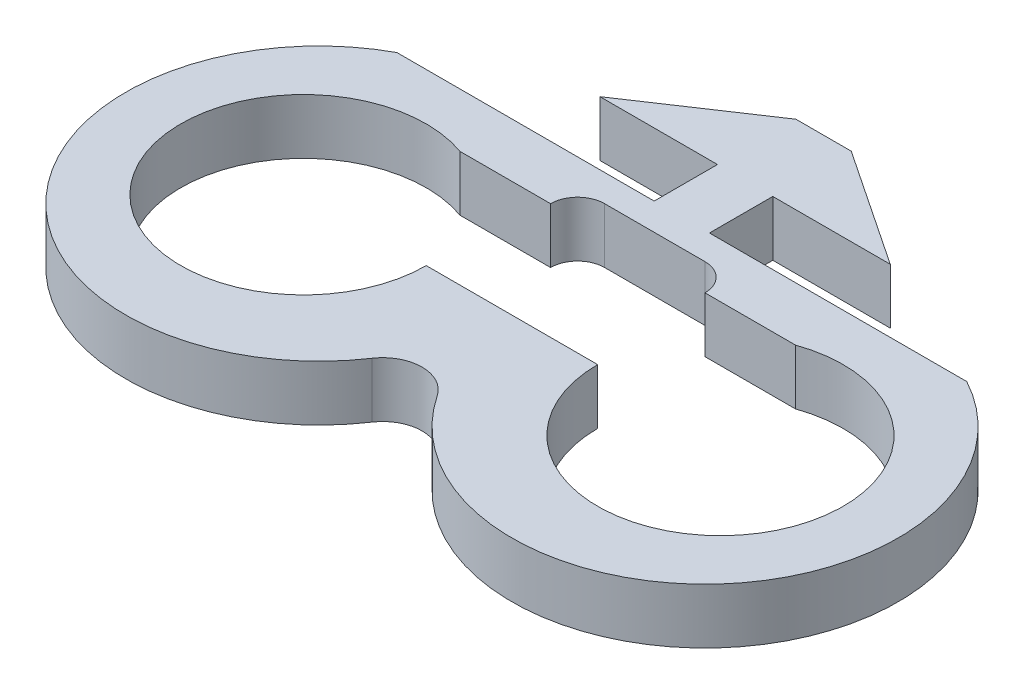
SolidWorks part; units mm, degrees
ref_plane "Front" through (0, 0, 0) normal (0, 0, 1) x (1, 0, 0)
ref_plane "Top" through (0, 0, 0) normal (0, 1, 0) x (1, 0, 0)
ref_plane "Right" through (0, 0, 0) normal (1, 0, 0) x (0, 0, -1)
sketch "Sketch1" plane through (0, 0, 0) normal (0, 1, 0) x (1, 0, 0)
  line L0 (-1.7907, 2.05) -> (-9.398, 2.05)
  line L2 (-1.7907, -2.05) -> (-1.7907, 2.05)
  line L4 (1.7907, -2.05) -> (1.7907, 2.05)
  line L7 (-9.398, 2.05) -> (-1.7907, 7.13)
  line L8 (-1.7907, 7.13) -> (1.7907, 7.13)
  line L9 (1.7907, 7.13) -> (9.398, 2.05)
  line L10 (9.398, 2.05) -> (1.7907, 2.05)
  line L11 (1.7907, -2.05) -> (25.0063, -2.05)
  line L12 (-1.7907, -2.05) -> (-25.0063, -2.05)
  line L13 (-25.0063, -2.05) -> (-25.0063, -13.0482)
  line L14 (-25.0063, -13.0482) -> (25.0063, -13.0482)
  line L15 (25.0063, -13.0482) -> (25.0063, -2.05)
  line L16 (25.0063, -2.05) -> (1.7907, -2.05)
  point P0 (0, 0)
  point P17 (0, 7.13)
  point P19 (0, -13.0482)
  point P24 (1.7907, 0)
  dimension "D1" = 18.796
  dimension "D2" = 3.5814
  dimension "D3" = 50.0126
  dimension "D4" = 10.9982
  dimension "D5" = 5.08
  dimension "D7" = 4.1
extrude "Boss-Extrude1" add sketch "Sketch1" along normal blind 3.5814 contours L14 L15 L11 L4 L10 L9 L8 L7 L0 L2 L12 L13
sketch "Sketch3" plane through (0, 3.5814, 0) normal (0, 1, 0) x (1, 0, 0)
  line L3 (-25.0063, -13.0482) -> (25.0063, -13.0482) construction
  line L16 (-25.0063, -13.0482) -> (25.0063, -13.0482)
  line L17 (25.0063, -13.0482) -> (25.0063, -2.05)
  line L18 (25.0063, -2.05) -> (1.7907, -2.05)
  line L19 (1.7907, -2.05) -> (1.7907, 2.05)
  line L20 (1.7907, 2.05) -> (9.398, 2.05)
  line L21 (9.398, 2.05) -> (1.7907, 7.13)
  line L22 (1.7907, 7.13) -> (-1.7907, 7.13)
  line L23 (-1.7907, 7.13) -> (-9.398, 2.05)
  line L24 (-9.398, 2.05) -> (-1.7907, 2.05)
  line L25 (-1.7907, 2.05) -> (-1.7907, -2.05)
  line L26 (-1.7907, -2.05) -> (-25.0063, -2.05)
  line L27 (-25.0063, -2.05) -> (-25.0063, -13.0482)
  line L28 (-25.0063, -13.0482) -> (25.0063, -13.0482)
  arc A2 (-25.0063, -13.0482) -> (-2.1111, -20.0005) centre (-12.5031, -13.0482) ccw
  arc A3 (2.1111, -20.0005) -> (25.0063, -13.0482) centre (12.5032, -13.0482) ccw
  arc A4 (2.1111, -20.0005) -> (-2.1111, -20.0005) centre (0, -21.4129) ccw
  point P14 (0, -13.0482)
  line M15 (-25.0063, -13.0482) -> (25.0063, -13.0482)
  dimension "D2" = 2.54
  dimension "D1" = 0
extrude "Boss-Extrude2" add sketch "Sketch3" against normal up to surface (3.5814 mm away) contours A2 M15 | L28 A3 up to face at (0, 0, 0.9864)
sketch "Sketch4" plane through (0, 3.5814, 0) normal (0, 1, 0) x (1, 0, 0)
  line L0 (-1025.0063, -13.0482) -> (48974.9937, -13.0482) construction
  circle A0 centre (-13.5, -13.0482) radius 7.95
  circle A1 centre (13.5, -13.0482) radius 7.95
  dimension "D1" = 15.9
  dimension "D2" = 13.5
  dimension "D3" = 13.5
extrude "Cut-Extrude2" cut sketch "Sketch4" against normal through all
sketch "Sketch5" plane through (0, 3.5814, 0) normal (0, 1, 0) x (1, 0, 0)
  line L2 (-3.25, -5.55) -> (3.25, -5.55) construction
  line L3 (-3.25, -3.8) -> (3.25, -3.8)
  line L5 (1.7907, -2.05) -> (25.0063, -2.05) construction
  line L8 (-5, -5.55) -> (-10.8581, -5.55)
  line L9 (5, -5.55) -> (10.8581, -5.55)
  line L10 (-5.55, -13.0482) -> (5.55, -13.0482)
  circle A0 centre (-13.5, -13.0482) radius 7.95 construction
  circle A1 centre (13.5, -13.0482) radius 7.95 construction
  arc A3 (-3.25, -3.8) -> (-5, -5.55) centre (-3.25, -5.55) ccw
  arc A4 (5, -5.55) -> (3.25, -3.8) centre (3.25, -5.55) ccw
  arc A8 (10.8581, -5.55) -> (5.55, -13.0482) centre (13.5, -13.0482) ccw
  arc A9 (-5.55, -13.0482) -> (-10.8581, -5.55) centre (-13.5, -13.0482) ccw
  point P7 (0, -5.55)
  point P12 (0, -15.5882)
  point P28 (0, -10.5082)
  dimension "D3" = 2.54
  dimension "D5" = 1.75
  dimension "D10" = 2.54
extrude "Cut-Extrude4" cut sketch "Sketch5" against normal up to next contours L8 A9 L10 A8 L9 A4 L3 A3
sketch "Sketch6" plane through (0, 3.5814, 0) normal (0, 1, 0) x (1, 0, 0)
  line L0 (-18.4503, -2.05) -> (-25.0063, -2.05)
  line L1 (-25.0063, -2.05) -> (-25.0063, -13.0482)
  line L2 (-1.7907, -2.05) -> (-25.0063, -2.05) construction
  line L3 (25.0063, -13.0482) -> (25.0063, -2.05)
  line L4 (25.0063, -2.05) -> (18.4503, -2.05)
  arc A0 (-18.4503, -2.05) -> (-25.0063, -13.0482) centre (-12.5031, -13.0482) ccw
  arc A1 (-25.0063, -13.0482) -> (-2.1111, -20.0005) centre (-12.5031, -13.0482) ccw construction
  arc A2 (25.0063, -13.0482) -> (18.4503, -2.05) centre (12.5032, -13.0482) ccw
  arc A3 (2.1111, -20.0005) -> (25.0063, -13.0482) centre (12.5032, -13.0482) ccw construction
extrude "Cut-Extrude5" cut sketch "Sketch6" against normal up to next
